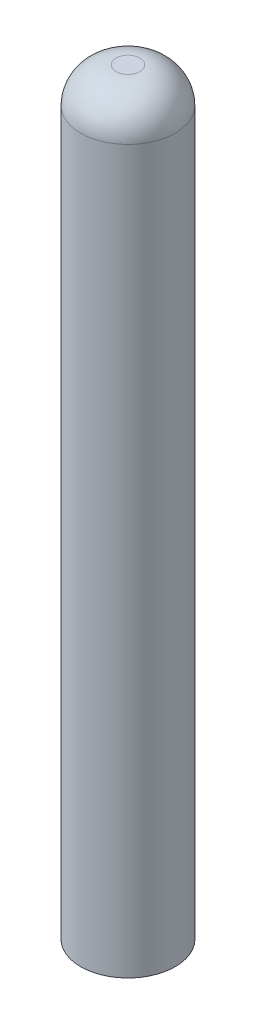
SolidWorks part; units mm, degrees
material "SS 304 (Default)"
ref_plane "Front Plane" through (0, 0, 0) normal (0, 0, 1) x (1, 0, 0)
ref_plane "Top Plane" through (0, 0, 0) normal (0, 1, 0) x (1, 0, 0)
ref_plane "Right Plane" through (0, 0, 0) normal (1, 0, 0) x (0, 0, -1)
sketch "Sketch1" plane through (0, 0, 0) normal (0, 1, 0) x (1, 0, 0)
  circle A0 centre (0, 0) radius 3.175
  dimension "D1" = 6.35
extrude "Extrude1" add sketch "Sketch1" along normal mid plane 50.8
fillet "Fillet1" radius 2.3813 1 edges at (0, 25.4, 3.175)
